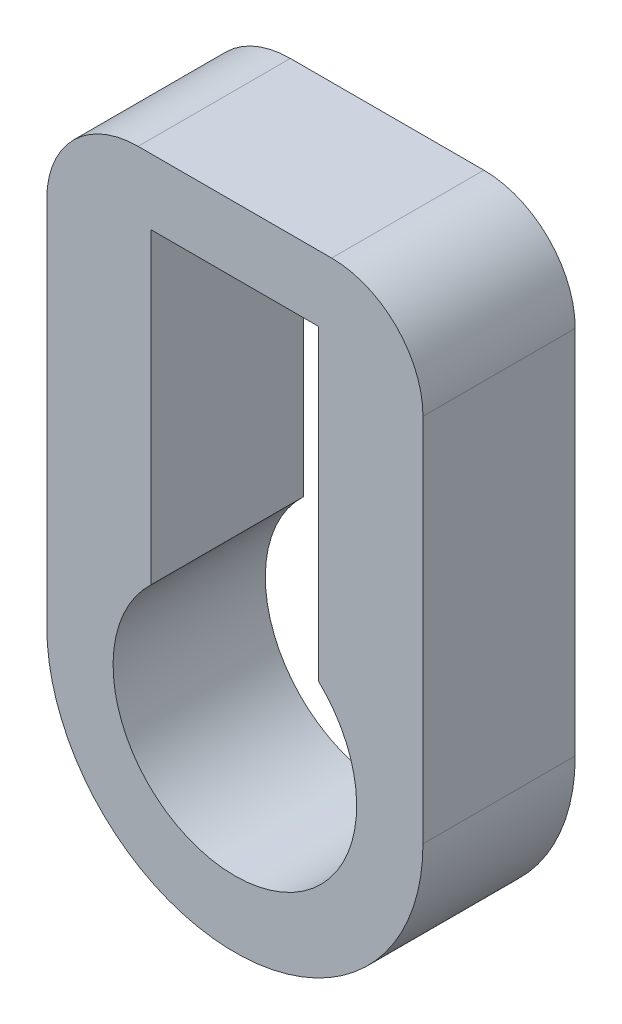
SolidWorks part; units mm, degrees
ref_plane "Front Plane" through (0, 0, 0) normal (0, 0, 1) x (1, 0, 0)
ref_plane "Top Plane" through (0, 0, 0) normal (0, 1, 0) x (1, 0, 0)
ref_plane "Right Plane" through (0, 0, 0) normal (1, 0, 0) x (0, 0, -1)
sketch "Sketch1" plane through (0, 0, 0) normal (0, 0, 1) x (1, 0, 0)
  line L1 (-0.6985, 3.302) -> (0.6985, 3.302)
  line L2 (-0.6985, 3.302) -> (-0.6985, 0)
  line L3 (-0.6985, 0) -> (0.6985, 0)
  line L4 (0.6985, 3.302) -> (0.6985, 0)
  line L5 (-1.569, 0) -> (1.569, 0)
  line L6 (-1.569, 0) -> (-1.569, 3.8505)
  line L7 (-1.569, 3.8505) -> (1.569, 3.8505)
  line L8 (1.569, 0) -> (1.569, 3.8505)
  circle A0 centre (0, 0) radius 0.6985
  circle A1 centre (0, 0) radius 1.569
extrude "Boss-Extrude1" add sketch "Sketch1" along normal blind 1.27 contours A1 L8 L7 L6 L2 L1 L4 | L5 A1 A0 | L5 A1 L4 | L2 A1 L5
sketch "Sketch2" plane through (0, 0, 0) normal (0, 0, -1) x (-1, 0, 0)
  circle A0 centre (0, 0) radius 1.016
extrude "Cut-Extrude1" cut sketch "Sketch2" against normal blind 2.54
fillet "Fillet2" radius 0.762 2 edges at (-1.569, 3.8505, 0.635) (1.569, 3.8505, 0.635)
